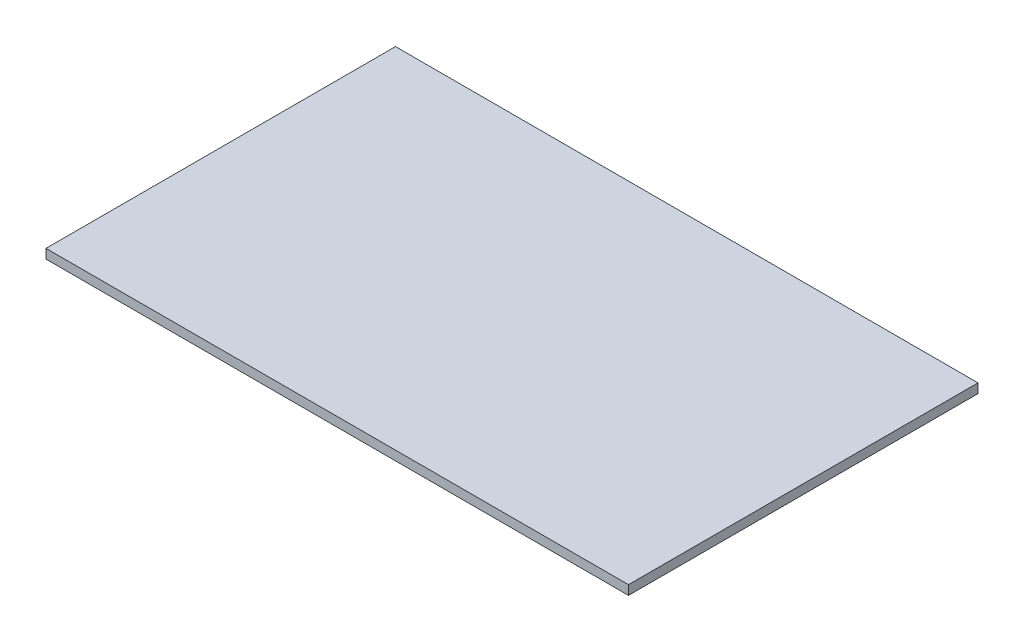
SolidWorks part; units mm, degrees
ref_plane "Front Plane" through (0, 0, 0) normal (0, 0, 1) x (1, 0, 0)
ref_plane "Top Plane" through (0, 0, 0) normal (0, 1, 0) x (1, 0, 0)
ref_plane "Right Plane" through (0, 0, 0) normal (1, 0, 0) x (0, 0, -1)
sketch "Sketch1" plane through (0, 0, 0) normal (0, 1, 0) x (1, 0, 0)
  line L1 (-50, -30) -> (50, -30)
  line L2 (-50, -30) -> (-50, 30)
  line L3 (-50, 30) -> (50, 30)
  line L4 (50, -30) -> (50, 30)
  line L5 (-50, -30) -> (50, 30) construction
  line L6 (-50, 30) -> (50, -30) construction
  point P0 (0, 0)
  dimension "D1" = 100
  dimension "D2" = 60
extrude "Boss-Extrude1" add sketch "Sketch1" along normal blind 1.6
